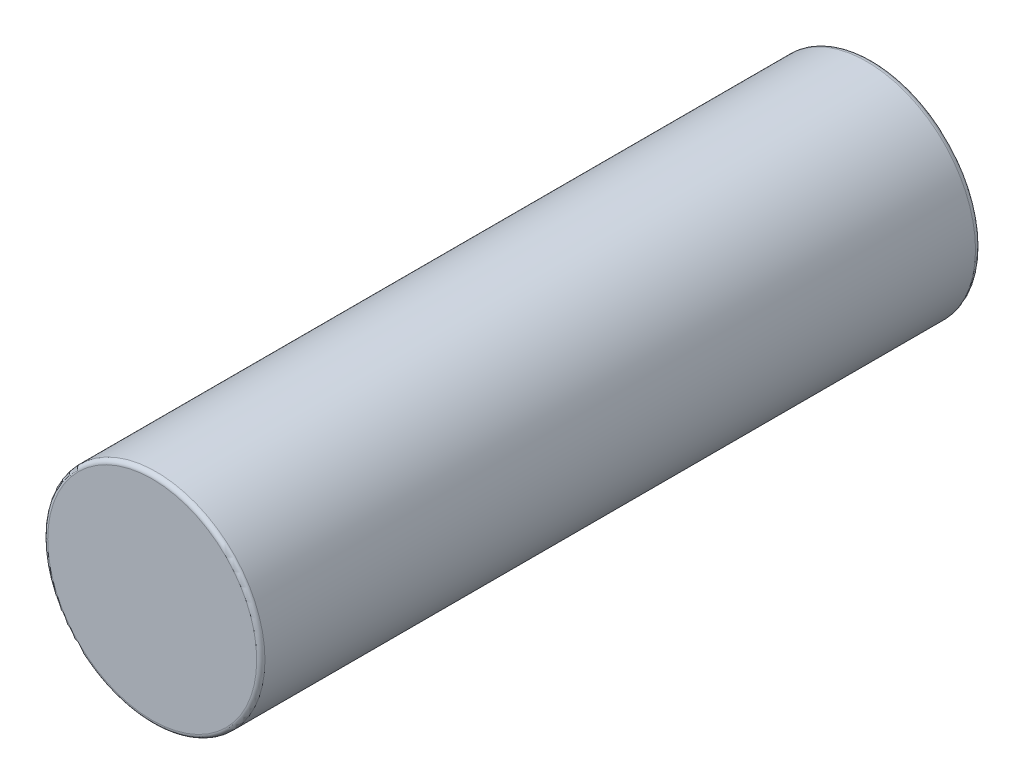
SolidWorks part; units mm, degrees
ref_plane "Front Plane" through (0, 0, 0) normal (0, 0, 1) x (1, 0, 0)
ref_plane "Top Plane" through (0, 0, 0) normal (0, 1, 0) x (1, 0, 0)
ref_plane "Right Plane" through (0, 0, 0) normal (1, 0, 0) x (0, 0, -1)
sketch "Sketch1" plane through (0, 0, 0) normal (0, 1, 0) x (1, 0, 0)
  line L0 (0, 0) -> (0, 70.09) construction
  line L1 (0, 70.09) -> (4.3922, 70.09)
  line L2 (4.5593, 69.9999) -> (5.4407, 68.6601)
  line L3 (5.6078, 68.57) -> (8.1, 68.57) construction
  line L4 (8.1, 68.57) -> (8.1, 69.27) construction
  line L6 (10.52, 69.21) -> (10.52, 0.4)
  line L7 (10.12, 0) -> (0, 0)
  line L8 (8.1, 69.156) -> (8.1, 68.97)
  line L9 (8.1, 68.97) -> (7.745, 68.97)
  line L10 (7.745, 68.97) -> (7.745, 68.57) construction
  line L11 (7.745, 68.97) -> (7.745, 68.67)
  line L12 (7.745, 68.67) -> (6.955, 68.67)
  line L13 (6.955, 68.67) -> (6.955, 68.57)
  line L14 (0, 69.79) -> (4.3383, 69.79)
  line L15 (4.3383, 69.79) -> (5.3383, 68.27)
  line L16 (6.955, 68.57) -> (5.6078, 68.57)
  line L17 (0, 70.09) -> (0, 69.79)
  line L18 (4.3383, 69.79) -> (5.1901, 68.4952) construction
  line L19 (5.3383, 68.27) -> (0, 68.27)
  line L20 (0, 68.27) -> (0, 0)
  arc A1 (9.94, 69.79) -> (10.52, 69.21) centre (9.94, 69.21) cw
  arc A2 (9.94, 69.79) -> (8.2011, 69.3298) centre (9.94, 66.2746) ccw
  arc A3 (5.4407, 68.6601) -> (5.6078, 68.57) centre (5.6078, 68.77) ccw
  arc A4 (4.3922, 70.09) -> (4.5593, 69.9999) centre (4.3922, 69.89) cw
  arc A5 (8.1, 69.156) -> (8.2011, 69.3298) centre (8.3, 69.156) cw
  arc A6 (4.3383, 69.79) -> (4.3383, 69.79) centre (4.3383, 69.79) cw
  arc A7 (10.52, 0.4) -> (10.12, 0) centre (10.12, 0.4) cw
  point P14 (5.5, 68.57)
  point P17 (4.5, 70.09)
  point P31 (0, 0)
  dimension "D10" = 0.58
  dimension "D11" = 0.2
  dimension "D14" = 0.2
  dimension "D18" = 0.3
  dimension "D19" = 0.4
  dimension "D1" = 21.04
  dimension "D2" = 70.09
  dimension "D3" = 9
  dimension "D4" = 11
  dimension "D5" = 0.3
  dimension "D6" = 0.58
  dimension "D7" = 2.42
  dimension "D8" = 1.22
  dimension "D9" = 0.7
  dimension "D12" = 0.3
  dimension "D13" = 7.745
  dimension "D15" = 13.91
  dimension "D16" = 0.2
  dimension "D17" = 0.3
revolve "Revolve1" add sketch "Sketch1" angle 360 about L0
sketch "Sketch2" plane through (0, 0, -70.09) normal (0, 0, -1) x (-1, 0, 0)
  line L0 (-1.65, 4.809) -> (1.65, 4.809) construction
  arc A2 (2.1512, 4.5732) -> (5.0361, -0.4236) centre (0, 0) cw construction
  arc A3 (5.5881, -0.47) -> (2.387, 5.0744) centre (0, 0) ccw
  arc A4 (4.4842, -0.3772) -> (1.9155, 4.072) centre (0, 0) ccw
  arc A5 (4.4842, -0.3772) -> (5.5881, -0.47) centre (5.0361, -0.4236) ccw
  arc A6 (2.387, 5.0744) -> (1.9155, 4.072) centre (2.1512, 4.5732) ccw
  circle A7 centre (0, 0) radius 4.5 construction
  arc A8 (2.8849, -4.1496) -> (-2.8849, -4.1496) centre (0, 0) cw construction
  arc A9 (-3.2011, -4.6044) -> (3.2011, -4.6044) centre (0, 0) ccw
  arc A10 (-2.5687, -3.6948) -> (2.5687, -3.6948) centre (0, 0) ccw
  arc A11 (-2.5687, -3.6948) -> (-3.2011, -4.6044) centre (-2.8849, -4.1496) ccw
  arc A12 (3.2011, -4.6044) -> (2.5687, -3.6948) centre (2.8849, -4.1496) ccw
  arc A13 (-5.0361, -0.4236) -> (-2.1512, 4.5732) centre (0, 0) cw construction
  arc A14 (-2.387, 5.0744) -> (-5.5881, -0.47) centre (0, 0) ccw
  arc A15 (-1.9155, 4.072) -> (-4.4842, -0.3772) centre (0, 0) ccw
  arc A16 (-1.9155, 4.072) -> (-2.387, 5.0744) centre (-2.1512, 4.5732) ccw
  arc A17 (-5.5881, -0.47) -> (-4.4842, -0.3772) centre (-5.0361, -0.4236) ccw
  circle A19 centre (0, 0) radius 5.6078 construction
  point P1 (1.4327, 1.9893)
  point P5 (4.3768, 2.527)
  point P12 (1.65, 4.809)
  point P13 (-1.65, 4.809)
  point P16 (0, -5.0539)
  point P23 (-4.3768, 2.527)
  point P28 (0, 0)
  point P29 (0, 0)
  point P30 (0, 0)
  dimension "D2" = 3.3
  dimension "D1" = 3
extrude "Cut-Extrude1" [suppressed] cut sketch "Sketch2" against normal up to surface (1.82 mm away)
sketch "Sketch3" plane through (0, 0, 0) normal (0, 0, 1) x (1, 0, 0)
  circle A0 centre (0, 0) radius 5.285
  circle A1 centre (0, 0) radius 5.54
  dimension "D1" = 10.57
  dimension "D2" = 11.08
extrude "Cut-Extrude2" [suppressed] cut sketch "Sketch3" against normal blind 0.28
ref_plane "Plane1" [suppressed] through (-10.52, 0, 0) normal (-1, 0, 0) x (0, 0, 1)
sketch "Sketch4" [suppressed] plane through (-10.52, 0, 0) normal (-1, 0, 0) x (0, 0, 1)
  line L0 (-16.87, 0) -> (-46.4484, 0) construction
  line L3 (-70.0584, 4.072) -> (-70.0584, -0.3772) construction
  text T0 "LGDBM502170\r\n" font "SWIsop1" height 3.5
  point P2 (0, 0)
  point P3 (-9.9726, 0)
  point P6 (0, 0)
  point P9 (0, 0)
  dimension "D1" = 23.61
  dimension "D2" = 16.87
extrude "Cut-Extrude3" [suppressed] cut sketch "Sketch4" against normal offset from surface (0.5217 mm away) 0.001
